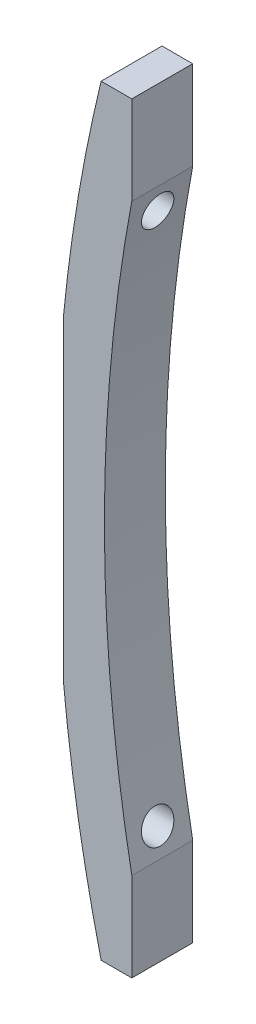
SolidWorks part; units mm, degrees
material "3.1325 (EN-AW 2017A)"
ref_plane "Plan de face" through (0, 0, 0) normal (0, 0, 1) x (1, 0, 0)
ref_plane "Plan de dessus" through (0, 0, 0) normal (0, 1, 0) x (1, 0, 0)
ref_plane "Plan de droite" through (0, 0, 0) normal (1, 0, 0) x (0, 0, -1)
sketch "Esquisse1" plane through (0, 0, 0) normal (0, 0, 1) x (1, 0, 0)
  line L0 (-202.4, -38.3437) -> (-202.4, -50)
  line L1 (-206.431, 50) -> (-202.4, 50)
  line L3 (-206.431, -50) -> (-202.4, -50)
  line L4 (-202.4, 50) -> (-202.4, 38.3437)
  arc A0 (-206.431, 50) -> (-206.431, -50) centre (0, 0) ccw
  arc A1 (-202.4, 38.3437) -> (-202.4, -38.3437) centre (0, 0) ccw
  dimension "D1" = 50
  dimension "D3" = 202.4
  dimension "D2" = 100
extrude "Boss.-Extru.1" add sketch "Esquisse1" along normal blind 8
hole_wizard "Trou taraudé M51" positions "Esquisse3" profile "Esquisse2" tap size "M5" standard "ISO" end condition through all
sketch "Esquisse3" plane through (-202.4, 0, 0) normal (1, 0, 0) x (0, 0, -1)
  line L0 (-8, 0) -> (0, 0) construction
  line L1 (-8, 38.3437) -> (-8, 50) construction
  point P0 (-4, 35)
  dimension "D1" = 35
  dimension "D2" = 4
sketch "Esquisse2" plane through (-202.4, 35, 4) normal (0, 1, 0) x (0, 0, -1)
  line L0 (0, 0) -> (0, 10)
  line L1 (0, 10) -> (2.1, 10)
  line L2 (2.1, 10) -> (2.1, 0)
  line L5 (2.1, 0) -> (0, 0)
  line L11 (0, -6.35) -> (0, 107.95) construction
  dimension "Diamètre du trou pour taraudage jusqu'au prochain" = 4.2
  dimension "Profondeur du trou pour taraudage jusqu'au prochain" = 10
cosmetic thread "Filetage de perçage1" parameters "D2"=5
hole_wizard "Trou taraudé M52" positions "Esquisse5" profile "Esquisse4" tap size "M5" standard "ISO" end condition through all
sketch "Esquisse5" plane through (-202.4, 0, 0) normal (1, 0, 0) x (0, 0, -1)
  line L0 (-8, 0) -> (0, 0) construction
  line L1 (0, 38.3437) -> (0, 50) construction
  point P0 (-4, -35)
  dimension "D1" = 35
  dimension "D2" = 4
sketch "Esquisse4" plane through (-202.4, -35, 4) normal (0, 1, 0) x (0, 0, -1)
  line L0 (0, 0) -> (0, 10)
  line L1 (0, 10) -> (2.1, 10)
  line L2 (2.1, 10) -> (2.1, 0)
  line L5 (2.1, 0) -> (0, 0)
  line L11 (0, -6.35) -> (0, 107.95) construction
  dimension "Diamètre du trou pour taraudage jusqu'au prochain" = 4.2
  dimension "Profondeur du trou pour taraudage jusqu'au prochain" = 10
cosmetic thread "Filetage de perçage2" parameters "D2"=5
sketch "Esquisse8" plane through (0, 0, 0) normal (0, 0, 1) x (1, 0, 0)
  line L0 (-202.4, 38.3437) -> (-202.4, 50) construction
  line L1 (-211.4, -48.4784) -> (-230.375, -48.4784)
  line L2 (-211.4, -48.4784) -> (-211.4, 47.6901)
  line L3 (-211.4, 47.6901) -> (-230.375, 47.6901)
  line L4 (-230.375, -48.4784) -> (-230.375, 47.6901)
  dimension "D1" = 9
extrude "Enlèv. mat.-Extru.1" cut sketch "Esquisse8" along normal blind 34
